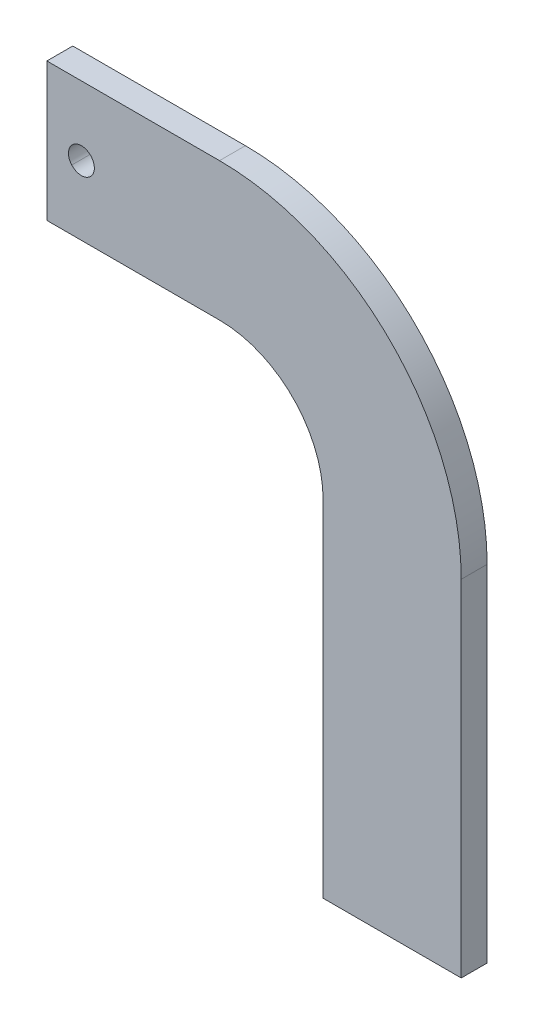
SolidWorks part; units mm, degrees
material "2014 Alloy"
ref_plane "Front Plane" through (0, 0, 0) normal (0, 0, 1) x (1, 0, 0)
ref_plane "Top Plane" through (0, 0, 0) normal (0, 1, 0) x (1, 0, 0)
ref_plane "Right Plane" through (0, 0, 0) normal (1, 0, 0) x (0, 0, -1)
sketch "Sketch3" plane through (0, 0, 0) normal (0, 0, 1) x (1, 0, 0)
  line L0 (0, 0) -> (101.6, 0)
  line L1 (101.6, 0) -> (101.6, 254)
  line L2 (0, 0) -> (0, 254)
  line L3 (-76.2, 330.2) -> (-203.2, 330.2)
  line L4 (-203.2, 330.2) -> (-203.2, 431.8)
  line L5 (-203.2, 431.8) -> (-76.2, 431.8)
  arc A0 (0, 254) -> (-76.2, 330.2) centre (-76.2, 254) ccw
  arc A1 (101.6, 254) -> (-76.2, 431.8) centre (-76.2, 254) ccw
  circle A2 centre (-177.8, 381) radius 9.525
  dimension "D3" = 127
  dimension "D4" = 330.2
  dimension "D7" = 19.05
  dimension "D6" = 101.6
  dimension "D8" = 50.8
  dimension "D1" = 101.6
  dimension "D2" = 254
  dimension "D5" = 254
  dimension "D9" = 25.4
extrude "Extrude1" add sketch "Sketch3" along normal blind 19.05
ref_plane "Plane1" through (0, 374.65, 0) normal (0, 1, 0) x (1, 0, 0)
split line "Split Line1"
